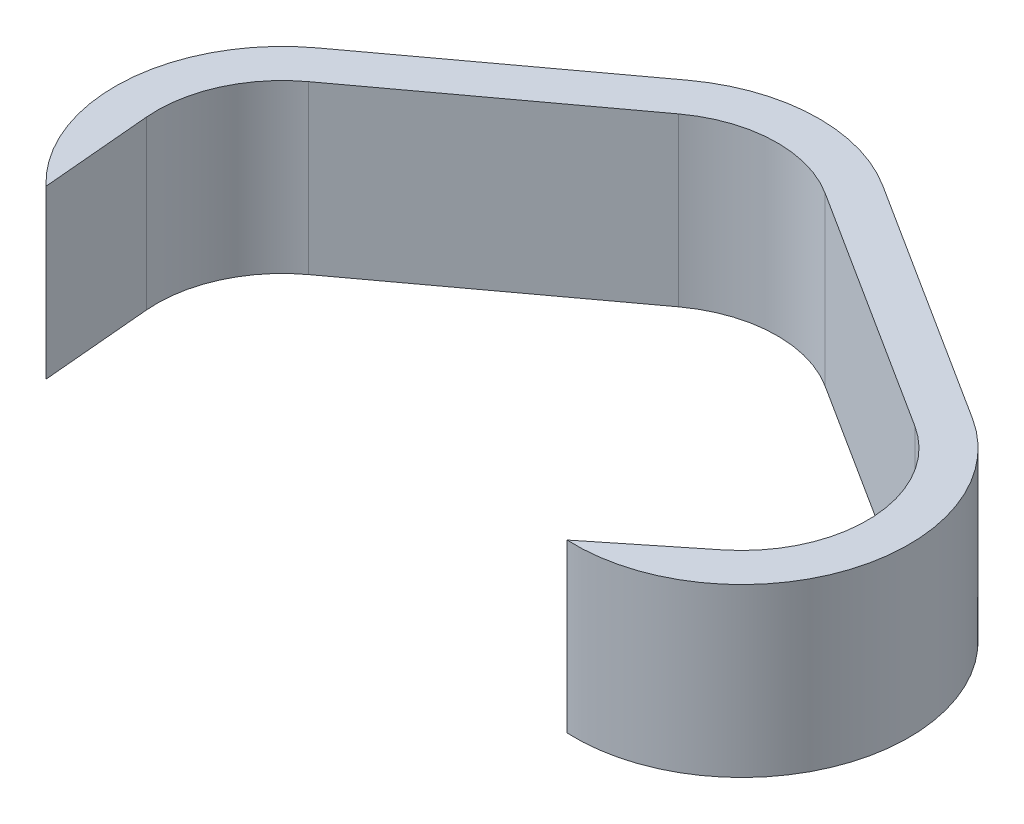
SolidWorks part; units mm, degrees
ref_plane "Front Plane" through (0, 0, 0) normal (0, 0, 1) x (1, 0, 0)
ref_plane "Top Plane" through (0, 0, 0) normal (0, 1, 0) x (1, 0, 0)
ref_plane "Right Plane" through (0, 0, 0) normal (1, 0, 0) x (0, 0, -1)
sketch "Sketch1" plane through (0, 0, 0) normal (0, 1, 0) x (1, 0, 0)
  line L0 (0, 0) -> (-27.7345, -76.2) construction
  line L1 (17.9011, -6.5155) -> (-9.8334, -82.7155)
  line L2 (-17.9011, 6.5155) -> (-45.6357, -69.6845)
  line L3 (0, 0) -> (37.5064, -23.8552) construction
  line L4 (13.6315, 21.4322) -> (51.138, -2.423)
  line L5 (-13.6315, -21.4322) -> (23.8749, -45.2874)
  line L6 (0, 0) -> (37.5064, -23.8552) construction
  line L7 (10.2237, 16.0742) -> (47.7301, -7.781)
  line L8 (-10.2237, -16.0742) -> (27.2828, -39.9294)
  line L9 (37.5064, -23.8552) -> (-32.3436, -23.8552) construction
  line L10 (0, 0) -> (0, 2.7601) construction
  line L11 (37.5064, -42.9052) -> (-32.3436, -42.9052)
  line L12 (37.5064, -4.8052) -> (-32.3436, -4.8052)
  line L13 (37.5064, -23.8552) -> (-32.3436, -23.8552) construction
  line L14 (37.5064, -49.2552) -> (-32.3436, -49.2552) construction
  line L15 (37.5064, 1.5448) -> (-32.3436, 1.5448) construction
  line L16 (0, 0) -> (-32.3436, -23.8552) construction
  line L17 (11.3075, -15.3311) -> (-21.036, -39.1863)
  line L18 (-11.3075, 15.3311) -> (-43.6511, -8.5241)
  line L19 (0, 0) -> (-32.3436, -23.8552) construction
  line L20 (15.0767, -20.4414) -> (-17.2669, -44.2966)
  line L21 (-15.0767, 20.4414) -> (-47.4203, -3.4138)
  line L22 (-32.3436, -23.8552) -> (-27.7345, -76.2) construction
  line L23 (-13.367, -22.1843) -> (-8.758, -74.5291)
  line L24 (-51.3202, -25.5261) -> (-46.7111, -77.8709)
  line L25 (-32.3436, -23.8552) -> (-27.7345, -76.2) construction
  line L26 (-7.0415, -21.6273) -> (-2.4324, -73.9721)
  line L27 (-57.6457, -26.0831) -> (-53.0366, -78.4279)
  line L28 (-27.7345, -76.2) -> (37.5064, -23.8552) construction
  line L29 (-39.6561, -61.3414) -> (25.5849, -8.9966)
  line L30 (-15.813, -91.0586) -> (49.428, -38.7138)
  line L31 (37.5064, -23.8552) -> (-27.7345, -76.2) construction
  line L32 (53.4018, -43.6667) -> (-11.8391, -96.0115)
  line L33 (21.611, -4.0437) -> (-43.6299, -56.3885)
  line L34 (0, 0) -> (-27.7345, -76.2) construction
  line L35 (23.8682, -8.6873) -> (-3.8663, -84.8873) construction
  line L36 (-23.8682, 8.6873) -> (-51.6027, -67.5127) construction
  circle A0 centre (0, 0) radius 22.225 construction
  circle A1 centre (0, 0) radius 25.4
  circle A2 centre (0, 0) radius 19.05
  arc A3 (17.9011, -6.5155) -> (-17.9011, 6.5155) centre (0, 0) ccw
  arc A4 (-45.6357, -69.6845) -> (-9.8334, -82.7155) centre (-27.7345, -76.2) ccw
  arc A5 (13.6315, 21.4322) -> (-13.6315, -21.4322) centre (0, 0) ccw
  arc A6 (23.8749, -45.2874) -> (51.138, -2.423) centre (37.5064, -23.8552) ccw
  arc A7 (10.2237, 16.0742) -> (-10.2237, -16.0742) centre (0, 0) ccw
  arc A8 (27.2828, -39.9294) -> (47.7301, -7.781) centre (37.5064, -23.8552) ccw
  arc A9 (37.5064, -42.9052) -> (37.5064, -4.8052) centre (37.5064, -23.8552) ccw
  arc A10 (-32.3436, -4.8052) -> (-32.3436, -42.9052) centre (-32.3436, -23.8552) ccw
  arc A11 (37.5064, -49.2552) -> (37.5064, 1.5448) centre (37.5064, -23.8552) ccw
  arc A12 (-32.3436, 1.5448) -> (-32.3436, -49.2552) centre (-32.3436, -23.8552) ccw
  arc A13 (11.3075, -15.3311) -> (-11.3075, 15.3311) centre (0, 0) ccw
  arc A14 (-43.6511, -8.5241) -> (-21.036, -39.1863) centre (-32.3436, -23.8552) ccw
  arc A15 (15.0767, -20.4414) -> (-15.0767, 20.4414) centre (0, 0) ccw
  arc A16 (-47.4203, -3.4138) -> (-17.2669, -44.2966) centre (-32.3436, -23.8552) ccw
  arc A17 (-13.367, -22.1843) -> (-51.3202, -25.5261) centre (-32.3436, -23.8552) ccw
  arc A18 (-46.7111, -77.8709) -> (-8.758, -74.5291) centre (-27.7345, -76.2) ccw
  arc A19 (-7.0415, -21.6273) -> (-57.6457, -26.0831) centre (-32.3436, -23.8552) ccw
  arc A20 (-53.0366, -78.4279) -> (-2.4324, -73.9721) centre (-27.7345, -76.2) ccw construction
  arc A21 (-39.6561, -61.3414) -> (-15.813, -91.0586) centre (-27.7345, -76.2) ccw
  arc A22 (49.428, -38.7138) -> (25.5849, -8.9966) centre (37.5064, -23.8552) ccw
  arc A23 (53.4018, -43.6667) -> (21.611, -4.0437) centre (37.5064, -23.8552) ccw construction
  arc A24 (-43.6299, -56.3885) -> (-11.8391, -96.0115) centre (-27.7345, -76.2) ccw construction
  arc A25 (23.8682, -8.6873) -> (-23.8682, 8.6873) centre (0, 0) ccw
  arc A26 (-51.6027, -67.5127) -> (-3.8663, -84.8873) centre (-27.7345, -76.2) ccw
  point P5 (-13.8673, -38.1)
  point P13 (18.7532, -11.9276)
  point P20 (18.7532, -11.9276)
  point P25 (2.5814, -23.8552)
  point P34 (2.5814, -23.8552)
  point P43 (-16.1718, -11.9276)
  point P48 (-16.1718, -11.9276)
  point P57 (-30.0391, -50.0276)
  point P62 (-30.0391, -50.0276)
  point P69 (4.8859, -50.0276)
  point P76 (4.8859, -50.0276)
  point P85 (-13.8673, -38.1)
  dimension "D1" = 44.45
  dimension "D2" = 3.175
  dimension "D3" = 3.175
  dimension "D4" = 20
  dimension "D5" = 76.2
  dimension "D6" = 122.458
  dimension "D7" = 44.45
  dimension "D8" = 69.85
extrude "Boss-Extrude1" add sketch "Sketch1" along normal blind 25.4
sketch "Sketch2" [suppressed] plane through (0, 0, 0) normal (0, 0, 1) x (1, 0, 0)
  line L0 (-10.6164, 11.5735) -> (-32.3347, -48.0969) construction
  line L1 (7.2847, 5.0581) -> (-14.4336, -54.6124) construction
  line L2 (-28.5176, 18.089) -> (-50.2359, -41.5815) construction
  line L3 (-10.6164, 11.5735) -> (26.89, -12.2817) construction
  line L4 (3.0151, 33.0058) -> (40.5215, 9.1506) construction
  line L5 (-24.248, -9.8587) -> (13.2584, -33.7139) construction
  line L6 (-10.6164, 11.5735) -> (26.89, -12.2817) construction
  line L7 (-0.3928, 27.6477) -> (37.1137, 3.7925) construction
  line L8 (-20.8401, -4.5006) -> (16.6663, -28.3558) construction
  line L9 (26.89, -12.2817) -> (-42.96, -12.2817) construction
  line L10 (-10.6164, 11.5735) -> (-10.6164, 14.3337) construction
  line L11 (26.89, -31.3317) -> (-42.96, -31.3317) construction
  line L12 (26.89, 6.7683) -> (-42.96, 6.7683) construction
  line L13 (26.89, -12.2817) -> (-42.96, -12.2817) construction
  line L14 (26.89, -37.6817) -> (-42.96, -37.6817) construction
  line L15 (26.89, 13.1183) -> (-42.96, 13.1183) construction
  line L16 (-41.6866, -11.3425) -> (-42.96, -12.2817) construction
  line L17 (-30.3791, -26.6736) -> (-31.6525, -27.6127) construction
  line L18 (-52.9942, 3.9886) -> (-54.2675, 3.0494) construction
  line L19 (-10.6164, 11.5735) -> (-42.96, -12.2817) construction
  line L20 (4.4603, -8.8679) -> (-27.8833, -32.7231) construction
  line L21 (-25.6931, 32.015) -> (-58.0367, 8.1598) construction
  line L22 (-42.96, -12.2817) -> (-32.3347, -48.0969) construction
  line L23 (-24.6968, -6.8635) -> (-14.0715, -42.6788) construction
  line L24 (-61.2233, -17.6998) -> (-50.598, -53.5151) construction
  line L25 (-42.96, -12.2817) -> (-32.3347, -48.0969) construction
  line L26 (-18.609, -5.0575) -> (-7.9837, -40.8727) construction
  line L27 (-67.311, -19.5059) -> (-56.6857, -55.3211) construction
  line L28 (-32.3347, -48.0969) -> (26.89, -12.2817) construction
  line L29 (-42.1926, -31.7958) -> (17.0321, 4.0194) construction
  line L30 (-22.4769, -64.398) -> (36.7478, -28.5827) construction
  line L31 (26.89, -12.2817) -> (-32.3347, -48.0969) construction
  line L32 (40.0338, -34.0164) -> (-19.1909, -69.8317) construction
  line L33 (13.7462, 9.4531) -> (-45.4785, -26.3622) construction
  line L34 (-13.0942, 4.7659) -> (-32.3347, -48.0969) construction
  line L35 (10.774, -3.9214) -> (-8.4665, -56.7842) construction
  line L36 (-36.9624, 13.4532) -> (-56.2029, -39.4096) construction
  line L37 (-58.0367, 8.1598) -> (-25.6931, 32.015)
  line L38 (3.0151, 33.0058) -> (40.5215, 9.1506)
  line L39 (40.0338, -34.0164) -> (-19.1909, -69.8317)
  line L40 (-56.6857, -55.3211) -> (-67.311, -19.5059)
  circle A0 centre (-10.6164, 11.5735) radius 22.225 construction
  circle A1 centre (-10.6164, 11.5735) radius 25.4 construction
  circle A2 centre (-10.6164, 11.5735) radius 19.05 construction
  arc A3 (7.2847, 5.0581) -> (-28.5176, 18.089) centre (-10.6164, 11.5735) ccw construction
  arc A4 (-50.2359, -41.5815) -> (-14.4336, -54.6124) centre (-32.3347, -48.0969) ccw construction
  arc A5 (3.0151, 33.0058) -> (-24.248, -9.8587) centre (-10.6164, 11.5735) ccw construction
  arc A6 (13.2584, -33.7139) -> (40.5215, 9.1506) centre (26.89, -12.2817) ccw construction
  arc A7 (-0.3928, 27.6477) -> (-20.8401, -4.5006) centre (-10.6164, 11.5735) ccw construction
  arc A8 (16.6663, -28.3558) -> (37.1137, 3.7925) centre (26.89, -12.2817) ccw construction
  arc A9 (26.89, -31.3317) -> (26.89, 6.7683) centre (26.89, -12.2817) ccw construction
  arc A10 (-42.96, 6.7683) -> (-42.96, -31.3317) centre (-42.96, -12.2817) ccw construction
  arc A11 (26.89, -37.6817) -> (26.89, 13.1183) centre (26.89, -12.2817) ccw construction
  arc A12 (-42.96, 13.1183) -> (-42.96, -37.6817) centre (-42.96, -12.2817) ccw construction
  arc A13 (-30.3791, -26.6736) -> (-52.9942, 3.9886) centre (-41.6866, -11.3425) ccw construction
  arc A14 (-54.2675, 3.0494) -> (-31.6525, -27.6127) centre (-42.96, -12.2817) ccw construction
  arc A15 (4.4603, -8.8679) -> (-25.6931, 32.015) centre (-10.6164, 11.5735) ccw construction
  arc A16 (-58.0367, 8.1598) -> (-27.8833, -32.7231) centre (-42.96, -12.2817) ccw construction
  arc A17 (-24.6968, -6.8635) -> (-61.2233, -17.6998) centre (-42.96, -12.2817) ccw construction
  arc A18 (-50.598, -53.5151) -> (-14.0715, -42.6788) centre (-32.3347, -48.0969) ccw construction
  arc A19 (-18.609, -5.0575) -> (-67.311, -19.5059) centre (-42.96, -12.2817) ccw construction
  arc A20 (-56.6857, -55.3211) -> (-7.9837, -40.8727) centre (-32.3347, -48.0969) ccw construction
  arc A21 (-42.1926, -31.7958) -> (-22.4769, -64.398) centre (-32.3347, -48.0969) ccw construction
  arc A22 (36.7478, -28.5827) -> (17.0321, 4.0194) centre (26.89, -12.2817) ccw construction
  arc A23 (40.0338, -34.0164) -> (13.7462, 9.4531) centre (26.89, -12.2817) ccw construction
  arc A24 (-45.4785, -26.3622) -> (-19.1909, -69.8317) centre (-32.3347, -48.0969) ccw construction
  arc A25 (10.774, -3.9214) -> (-36.9624, 13.4532) centre (-13.0942, 4.7659) ccw construction
  arc A26 (-56.2029, -39.4096) -> (-8.4665, -56.7842) centre (-32.3347, -48.0969) ccw construction
  arc A27 (-67.311, -19.5059) -> (-58.0367, 8.1598) centre (-42.96, -12.2817) cw
  arc A28 (-25.6931, 32.015) -> (3.0151, 33.0058) centre (-10.6164, 11.5735) cw
  arc A29 (40.5215, 9.1506) -> (40.0338, -34.0164) centre (26.89, -12.2817) cw
  arc A30 (-19.1909, -69.8317) -> (-56.6857, -55.3211) centre (-32.3347, -48.0969) cw
  point P5 (-21.4756, -18.2617)
  point P13 (8.1368, -0.3541)
  point P20 (8.1368, -0.3541)
  point P25 (-8.035, -12.2817)
  point P34 (-8.035, -12.2817)
  point P43 (-42.3233, -11.8121)
  point P48 (-26.7882, -0.3541)
  point P57 (-37.6474, -30.1893)
  point P62 (-37.6474, -30.1893)
  point P69 (-2.7224, -30.1893)
  point P76 (-2.7224, -30.1893)
  point P85 (-22.7145, -21.6655)
  dimension "D1" = 44.45
  dimension "D2" = 3.175
  dimension "D3" = 3.175
  dimension "D4" = 20
  dimension "D5" = 63.5
  dimension "D6" = 122.458
  dimension "D7" = 44.45
  dimension "D8" = 69.85
extrude "Boss-Extrude2" [suppressed] add sketch "Sketch2" along normal blind 6.35
